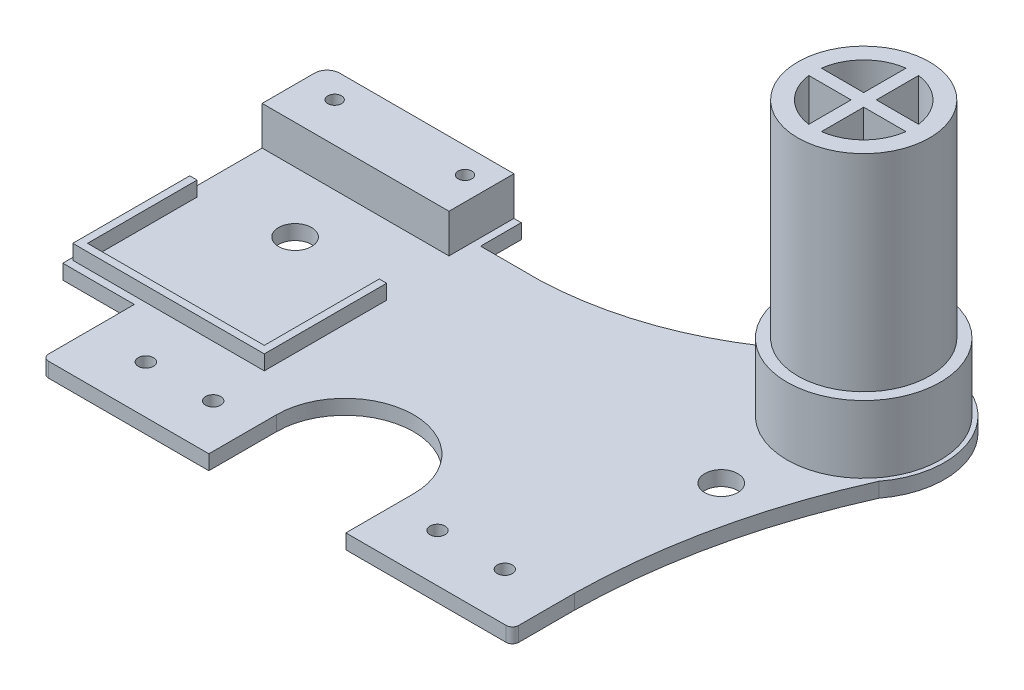
SolidWorks part; units mm, degrees
ref_plane "Front Plane" through (0, 0, 0) normal (0, 0, 1) x (1, 0, 0)
ref_plane "Top Plane" through (0, 0, 0) normal (0, 1, 0) x (1, 0, 0)
ref_plane "Right Plane" through (0, 0, 0) normal (1, 0, 0) x (0, 0, -1)
sketch "Sketch1" plane through (0, 0, 0) normal (0, 1, 0) x (1, 0, 0)
  line L1 (-55.85, 37.5) -> (55.85, 37.5)
  line L2 (-55.85, 37.5) -> (-55.85, -36)
  line L3 (-54.35, -37.5) -> (54.35, -37.5)
  line L4 (55.85, 37.5) -> (55.85, -36)
  line L5 (-55.85, 37.5) -> (55.85, -37.5) construction
  line L6 (-55.85, -37.5) -> (55.85, 37.5) construction
  arc A0 (-55.85, -36) -> (-54.35, -37.5) centre (-54.35, -36) ccw
  arc A1 (55.85, -36) -> (54.35, -37.5) centre (54.35, -36) cw
  point P0 (0, 0)
  dimension "D3" = 1.5
  dimension "D4" = 1.5
  dimension "D1" = 111.7
  dimension "D2" = 75
extrude "Boss-Extrude1" add sketch "Sketch1" along normal blind 3.5
sketch "Sketch2" plane through (0, 3.5, 0) normal (0, 1, 0) x (1, 0, 0)
  line L0 (0, -37.5) -> (0, -5.3707) construction
  line L1 (-54.35, -37.5) -> (54.35, -37.5) construction
  line L2 (-42.65, -26.1026) -> (-26.65, -26.1026) construction
  line L3 (-16.275, -37.5) -> (-16.275, -21.4097)
  line L5 (-54.35, -37.5) -> (54.35, -37.5) construction
  line L6 (16.275, -37.5) -> (16.275, -21.4097)
  line L7 (-16.275, -37.5) -> (16.275, -37.5)
  circle A0 centre (-42.65, -26.1026) radius 1.8
  circle A1 centre (-26.65, -26.1026) radius 1.8
  circle A2 centre (26.65, -26.1026) radius 1.8
  circle A3 centre (42.65, -26.1026) radius 1.8
  circle A4 centre (-50.6288, 17.3368) radius 3.9201
  circle A5 centre (50.6288, 17.3368) radius 3.9201
  arc A6 (-16.275, -21.4097) -> (16.275, -21.4097) centre (0, -21.4097) cw
  dimension "D1" = 3.6
  dimension "D3" = 3.6
  dimension "D2" = 16
extrude "Cut-Extrude1" cut sketch "Sketch2" against normal blind 4
sketch "Sketch3" plane through (0, 0, 0) normal (0, 1, 0) x (1, 0, 0)
  line L0 (55.85, 37.5) -> (48.3453, 74.6317) construction
  circle A0 centre (53.7066, 48.105) radius 15
  dimension "D1" = 30
extrude "Boss-Extrude2" add sketch "Sketch3" along normal blind 3.5
sketch "Sketch4" plane through (0, 3.5, 0) normal (0, 1, 0) x (1, 0, 0)
  circle A0 centre (53.7066, 48.105) radius 15
  dimension "D1" = 30
extrude "Boss-Extrude3" add sketch "Sketch4" along normal blind 65
sketch "Sketch5" plane through (0, 68.5, 0) normal (0, 1, 0) x (1, 0, 0)
  line L0 (53.7066, 33.105) -> (53.7066, 55.0108) construction
  line L1 (38.7066, 48.105) -> (66.1233, 48.105) construction
  line L2 (52.2066, 59.6499) -> (52.2066, 49.605)
  line L3 (55.2066, 59.6499) -> (55.2066, 49.605)
  line L4 (42.1617, 49.605) -> (52.2066, 49.605)
  line L5 (42.1617, 46.605) -> (52.2066, 46.605)
  line L6 (55.2066, 46.605) -> (65.2515, 46.605)
  line L7 (52.2066, 46.605) -> (52.2066, 36.5601)
  line L8 (55.2066, 49.605) -> (65.2515, 49.605)
  line L9 (55.2066, 46.605) -> (55.2066, 36.5601)
  circle A0 centre (53.7066, 48.105) radius 15 construction
  arc A1 (42.1617, 46.605) -> (52.2066, 36.5601) centre (53.7066, 48.105) ccw
  arc A2 (53.7066, 36.463) -> (65.2515, 46.605) centre (53.7066, 48.105) ccw
  arc A3 (65.2515, 49.605) -> (55.2066, 59.6499) centre (53.7066, 48.105) ccw
  arc A4 (52.2066, 59.6499) -> (42.1617, 49.605) centre (53.7066, 48.105) ccw
  dimension "D1" = 1.5
  dimension "D2" = 1.5
extrude "Cut-Extrude2" cut sketch "Sketch5" against normal blind 45 contours L5 A1 L7 | L9 A2 L6 | L8 A3 L3 | L2 A4 L4
sketch "Sketch7" plane through (0, 0, 0) normal (0, 1, 0) x (1, 0, 0)
  line L0 (53.7066, 48.105) -> (84.7143, 79.1126) construction
  line L1 (55.85, -36) -> (55.85, 33.2589) construction
  line L2 (43.0984, 37.5) -> (-55.85, 37.5) construction
  line L3 (-12.4774, 37.5) -> (55.85, 37.5)
  line L4 (55.85, -22.7272) -> (55.85, 37.5)
  arc A0 (68.9624, 36.4272) -> (37.9036, 59.0308) centre (53.7066, 48.105) ccw
  arc A1 (55.85, -22.7272) -> (68.9624, 36.4272) centre (206.4841, -25.087) cw
  arc A2 (37.9036, 59.0308) -> (-12.4774, 37.5) centre (-15.4648, 114.2003) cw
extrude "Boss-Extrude4" add sketch "Sketch7" along normal blind 3.5
sketch "Sketch8" plane through (0, 3.5, 0) normal (0, 1, 0) x (1, 0, 0)
  circle A0 centre (53.7066, 48.105) radius 18.2022
extrude "Boss-Extrude5" add sketch "Sketch8" along normal blind 16
sketch "Sketch9" plane through (0, 68.5, 0) normal (0, 1, 0) x (1, 0, 0)
  circle A0 centre (53.7066, 48.105) radius 14
  circle A1 centre (53.7066, 48.105) radius 15.7762
  dimension "D1" = 28
extrude "Cut-Extrude3" cut sketch "Sketch9" against normal blind 49
sketch "Sketch11" plane through (0, 0, 0) normal (0, 1, 0) x (1, 0, 0)
  line L0 (-55.85, 37.5) -> (-67.8414, 37.5)
  line L1 (-72.8414, 32.5) -> (-72.8414, -9.6318)
  line L3 (-55.85, 37.5) -> (-55.85, -36) construction
  line L4 (-55.85, 0) -> (-55.85, 37.5)
  line L6 (-55.85, -14.6318) -> (-55.85, 0)
  line L7 (-55.85, -15.6318) -> (-55.85, -14.6318)
  line L8 (-66.8414, -15.6318) -> (-55.85, -15.6318)
  line L9 (-72.8414, -9.6318) -> (-72.8414, -15.6318)
  line L10 (-72.8414, -15.6318) -> (-66.8414, -15.6318)
  line L11 (-67.8414, 37.5) -> (-72.8414, 37.5)
  line L12 (-72.8414, 37.5) -> (-72.8414, 32.5)
extrude "Boss-Extrude6" add sketch "Sketch11" along normal blind 3.5
sketch "Sketch12" plane through (0, 3.5, 0) normal (0, 1, 0) x (1, 0, 0)
  line L1 (-28.4914, 15.21) -> (-26.7414, 15.21)
  line L4 (-26.7414, -13.861) -> (-26.7414, 15.21)
  line L5 (-72.2414, -13.861) -> (-26.7414, -13.861)
  line L6 (-72.2414, -13.861) -> (-72.2414, 13.9289)
  line L7 (-71.4914, 13.9289) -> (-72.2414, 13.9289)
  line L9 (-28.4914, 26.953) -> (-28.4914, 30.5898) construction
  line L12 (-70.4914, -12.111) -> (-70.4914, 13.9289)
  line L13 (-70.4914, -12.111) -> (-28.4914, -12.111)
  line L14 (-28.4914, -12.111) -> (-28.4914, 15.21)
  line L15 (-71.4914, 13.9289) -> (-70.4914, 13.9289)
  dimension "D1" = 1.75
extrude "Boss-Extrude7" add sketch "Sketch12" along normal blind 3.5
sketch "Sketch13" plane through (0, 0, 0) normal (0, 1, 0) x (1, 0, 0)
  line L1 (-72.8414, 37.5) -> (-26.7134, 37.5)
  line L2 (-72.8414, 37.5) -> (-72.8414, 47.1619)
  line L3 (-72.8414, 47.1619) -> (-26.7134, 47.1619)
  line L4 (-26.7134, 37.5) -> (-26.7134, 47.1619)
extrude "Boss-Extrude8" add sketch "Sketch13" along normal blind 3.5
sketch "Sketch14" plane through (0, 3.5, 0) normal (0, 1, 0) x (1, 0, 0)
  line L1 (-72.8414, 47.1619) -> (-28.4507, 47.1619)
  line L2 (-72.8414, 47.1619) -> (-72.8414, 31.7269)
  line L3 (-72.8414, 31.7269) -> (-28.4507, 31.7269)
  line L4 (-28.4507, 47.1619) -> (-28.4507, 31.7269)
  dimension "D1" = 15.435
extrude "Boss-Extrude9" add sketch "Sketch14" along normal blind 9.2
sketch "Sketch15" plane through (0, 12.7, 0) normal (0, 1, 0) x (1, 0, 0)
  line L0 (-72.8414, 41.0904) -> (-64.9664, 41.0904) construction
  line L1 (-72.8414, 47.1619) -> (-72.8414, 31.7269) construction
  line L2 (-28.4507, 47.1619) -> (-72.8414, 47.1619) construction
  line L3 (-64.9664, 41.0904) -> (-34.0164, 41.0904) construction
  circle A0 centre (-64.9664, 41.0904) radius 1.625
  circle A1 centre (-34.0164, 41.0904) radius 1.625
  dimension "D3" = 3.25
  dimension "D5" = 3.25
  dimension "D1" = 7.875
  dimension "D2" = 6.0716
  dimension "D4" = 30.95
extrude "Cut-Extrude4" cut sketch "Sketch15" against normal up to next
fillet "Fillet3" radius 3 1 edges at (-72.8414, 6.35, -47.1619)
sketch "Sketch16" plane through (0, 19.5, 0) normal (0, 1, 0) x (1, 0, 0)
  circle A0 centre (53.7066, 48.105) radius 15.65
  circle A1 centre (53.7066, 48.105) radius 14
  dimension "D1" = 31.3
extrude "Boss-Extrude10" add sketch "Sketch16" along normal up to surface (49 mm away) up to face at (48.2884, 68.5, -53.5231)
